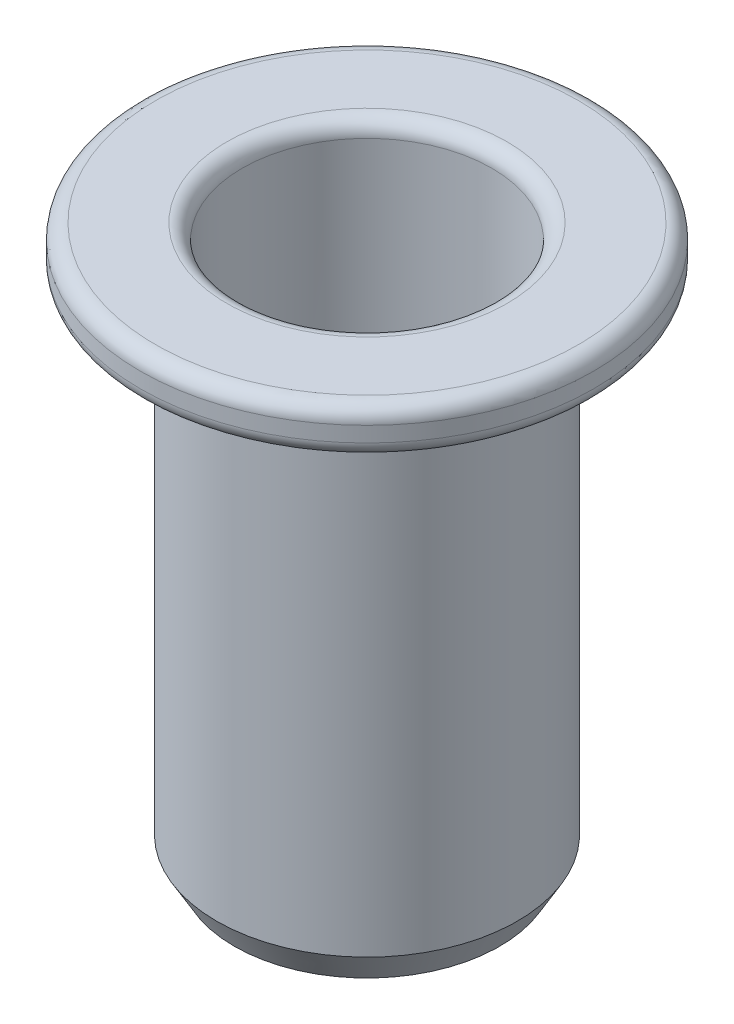
SolidWorks part; units mm, degrees
ref_plane "Front Plane" through (0, 0, 0) normal (0, 0, 1) x (1, 0, 0)
ref_plane "Top Plane" through (0, 0, 0) normal (0, 1, 0) x (1, 0, 0)
ref_plane "Right Plane" through (0, 0, 0) normal (1, 0, 0) x (0, 0, -1)
sketch "Sketch1" plane through (0, 0, 0) normal (0, 0, 1) x (1, 0, 0)
  line L0 (0, 0) -> (0, -4.7384) construction
  line L1 (2.45, 0) -> (4.45, 0)
  line L2 (4.45, 0) -> (4.45, -0.9)
  line L3 (4.45, -0.9) -> (2.95, -0.9)
  line L4 (2.95, -0.9) -> (2.95, -11)
  line L5 (2.95, -11) -> (2, -11)
  line L6 (2, -11) -> (2, -4.9)
  line L7 (2, -4.9) -> (2.45, -4.9)
  line L8 (2.45, -4.9) -> (2.45, 0)
  dimension "D1" = 8.9
  dimension "D2" = 5.9
  dimension "D3" = 0.9
  dimension "D4" = 11
  dimension "D5" = 4.9
  dimension "D6" = 4.9
  dimension "D7" = 4
revolve "Revolve1" add sketch "Sketch1" angle 360 about L0
fillet "Fillet1" radius 0.3 3 edges at (0, -0.9, 4.45) (0, 0, 4.45) (0, 0, 2.45)
chamfer "Chamfer1" distance 0.6 angle 30 1 edges at (0, -11, 2.95)
chamfer "Chamfer2" distance 0.5 angle 30 1 edges at (0, -11, 2)
